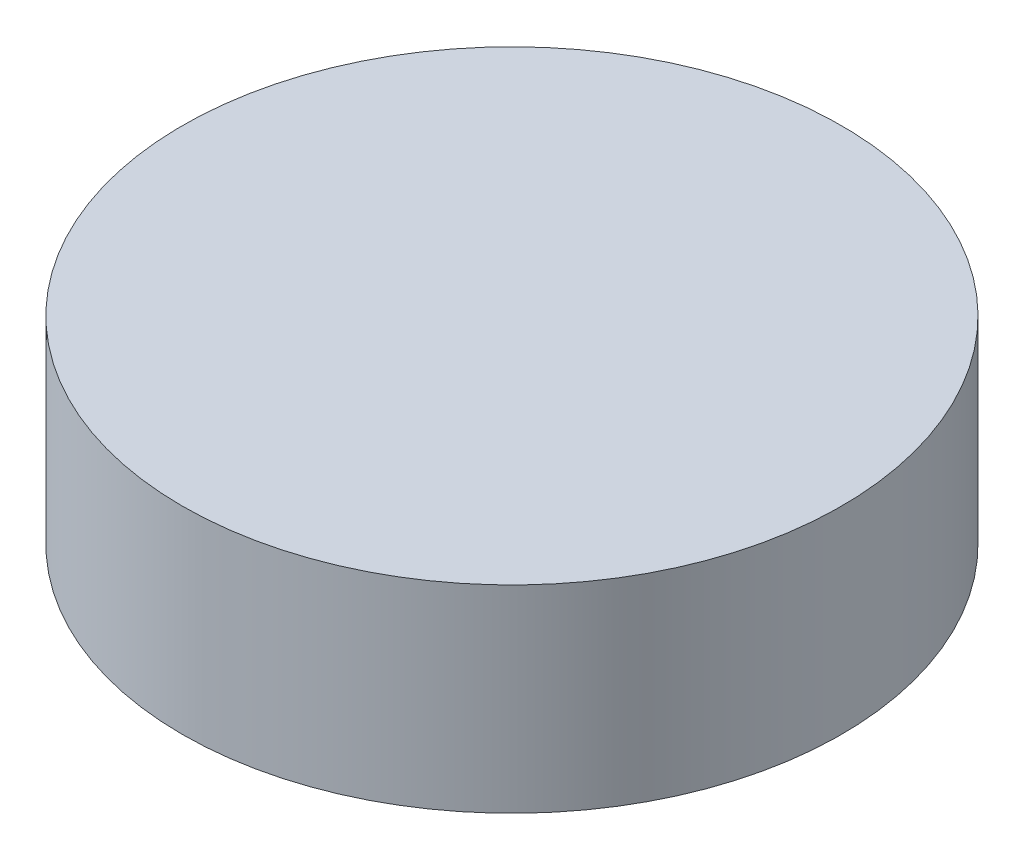
SolidWorks part; units mm, degrees
ref_plane "Front" through (0, 0, 0) normal (0, 0, 1) x (1, 0, 0)
ref_plane "Top" through (0, 0, 0) normal (0, 1, 0) x (1, 0, 0)
ref_plane "Right" through (0, 0, 0) normal (1, 0, 0) x (0, 0, -1)
sketch "草图1" plane through (0, 0, 0) normal (0, 1, 0) x (1, 0, 0)
  circle A0 centre (0, 0) radius 50
  dimension "D1" = 100
extrude "凸台-拉伸1" add sketch "草图1" along normal blind 30
